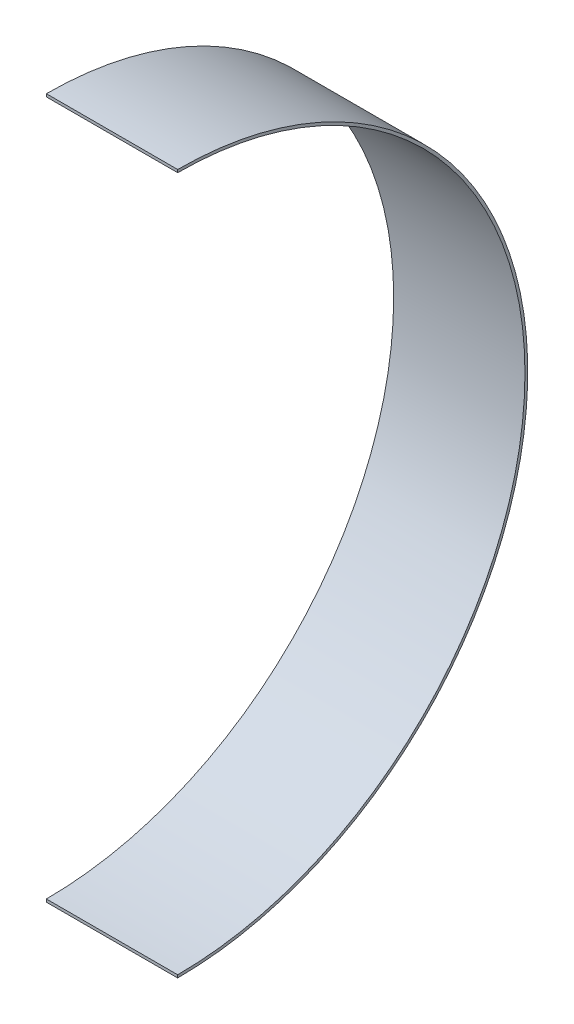
SolidWorks part; units mm, degrees
ref_plane "Front Plane" through (0, 0, 0) normal (0, 0, 1) x (1, 0, 0)
ref_plane "Top Plane" through (0, 0, 0) normal (0, 1, 0) x (1, 0, 0)
ref_plane "Right Plane" through (0, 0, 0) normal (1, 0, 0) x (0, 0, -1)
sketch "Sketch1" plane through (0, 0, 0) normal (1, 0, 0) x (0, 0, -1)
  line L0 (0, 200) -> (0, -200)
  circle A0 centre (0, 0) radius 200
  circle A1 centre (0, 0) radius 198.4
extrude "Boss-Extrude1" add sketch "Sketch1" along normal blind 75 contours A1 L0 A0
